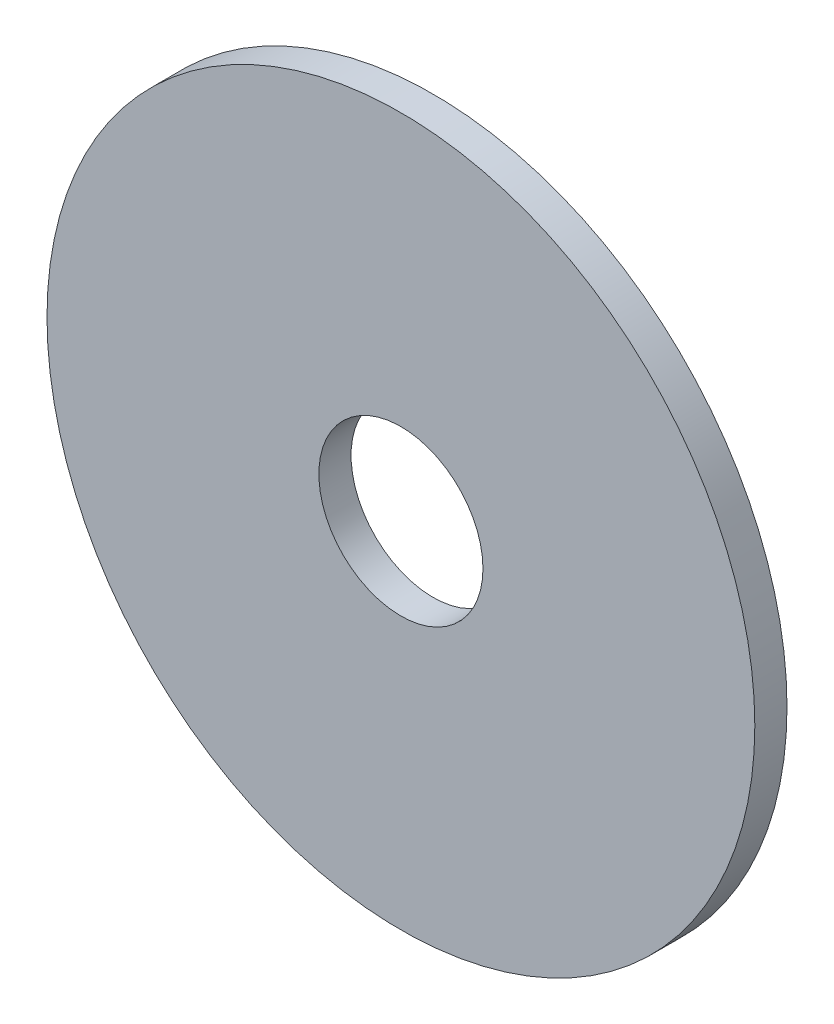
SolidWorks part; units mm, degrees
material "Acier non allié"
ref_plane "Plan de face" through (0, 0, 0) normal (0, 0, 1) x (1, 0, 0)
ref_plane "Plan de dessus" through (0, 0, 0) normal (0, 1, 0) x (1, 0, 0)
ref_plane "Plan de droite" through (0, 0, 0) normal (1, 0, 0) x (0, 0, -1)
sketch "Esquisse1" plane through (0, 0, 0) normal (0, 0, 1) x (1, 0, 0)
  circle A0 centre (0, 0) radius 25.5
  circle A1 centre (0, 0) radius 110
  dimension "D1" = 51
  dimension "D2" = 220
extrude "Boss.-Extru.1" add sketch "Esquisse1" along normal blind 10
